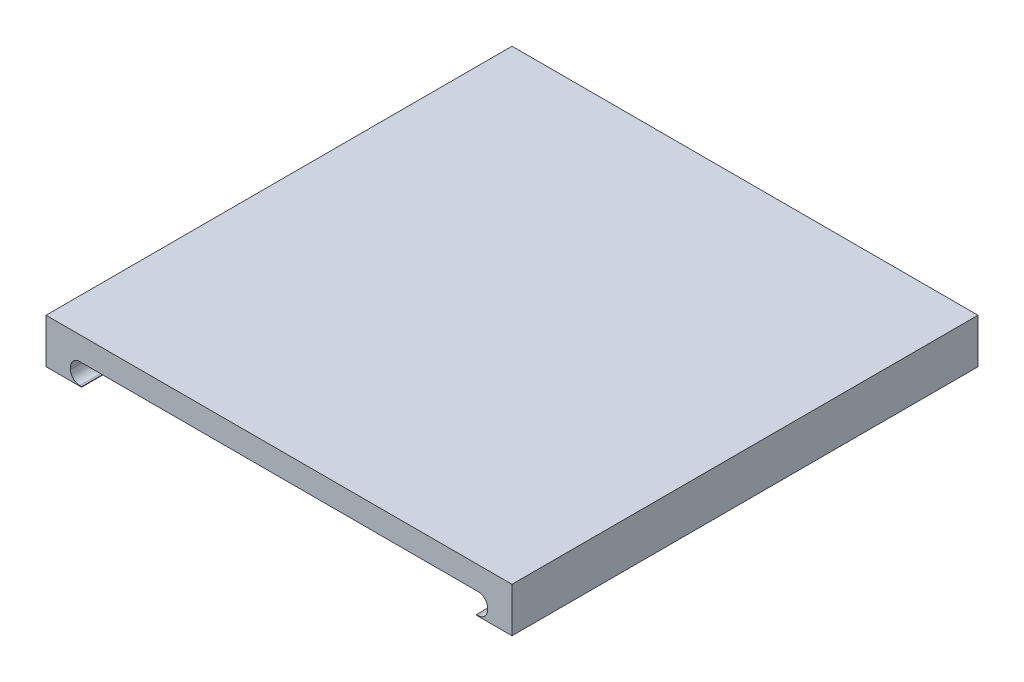
SolidWorks part; units mm, degrees
ref_plane "Front Plane" through (0, 0, 0) normal (0, 0, 1) x (1, 0, 0)
ref_plane "Top Plane" through (0, 0, 0) normal (0, 1, 0) x (1, 0, 0)
ref_plane "Right Plane" through (0, 0, 0) normal (1, 0, 0) x (0, 0, -1)
sketch "Sketch2" plane through (0, 0, 0) normal (0, 1, 0) x (1, 0, 0)
  line L7 (-25, -25) -> (25, -25)
  line L8 (-25, -25) -> (-25, 25)
  line L9 (-25, 25) -> (25, 25)
  line L10 (25, -25) -> (25, 25)
  line L11 (-25, -25) -> (25, 25) construction
  line L12 (-25, 25) -> (25, -25) construction
  point P0 (0, 0)
extrude "Boss-Extrude1" add sketch "Sketch2" along normal blind 5
sketch "Sketch4" plane through (0, 0, -25) normal (0, 0, -1) x (-1, 0, 0)
  line L2 (0, 0) -> (0, 5) construction
  line L3 (-25, 5) -> (25, 5) construction
sketch "Sketch6" plane through (0, 0, -25) normal (0, 0, -1) x (-1, 0, 0)
  line L0 (0, 0) -> (0, 1.25) construction
  line L13 (-25, 0) -> (25, 0) construction
  line L14 (-21.1824, 2.5) -> (21.1824, 2.5)
  line L15 (-21.1824, 2.5) -> (-21.1824, 0)
  line L16 (-21.1824, 0) -> (21.1824, 0)
  line L17 (21.1824, 2.5) -> (21.1824, 0)
  line L18 (-21.1824, 2.5) -> (21.1824, 0) construction
  line L19 (-21.1824, 0) -> (21.1824, 2.5) construction
extrude "Cut-Extrude1" cut sketch "Sketch6" against normal blind 50
sketch "Sketch9" plane through (0, 0, -25) normal (0, 0, -1) x (-1, 0, 0)
  line L1 (-21.1824, 2.5) -> (-22.371, 2.5)
  line L2 (-21.1824, 2.5) -> (-21.1824, 0.2785)
  line L3 (-21.1824, 0.2785) -> (-22.371, 0.2785)
  line L4 (-22.371, 2.5) -> (-22.371, 0.2785)
extrude "Cut-Extrude3" cut sketch "Sketch9" against normal blind 50
fillet "Fillet2" radius 1 1 edges at (22.371, 2.5, 0)
fillet "Fillet3" radius 1 1 edges at (22.371, 0.2785, 0)
sketch "Sketch11" plane through (0, 0, 25) normal (0, 0, 1) x (1, 0, 0)
  line L1 (-21.1824, 2.5) -> (-22.371, 2.5)
  line L2 (-21.1824, 2.5) -> (-21.1824, 0.2785)
  line L3 (-21.1824, 0.2785) -> (-22.371, 0.2785)
  line L4 (-22.371, 2.5) -> (-22.371, 0.2785)
extrude "Cut-Extrude4" cut sketch "Sketch11" against normal blind 50
fillet "Fillet5" radius 1 1 edges at (-22.371, 2.5, 0)
fillet "Fillet6" radius 1 1 edges at (-22.371, 0.2785, 0)
sketch "Sketch13" plane through (0, 0, 25) normal (0, 0, 1) x (1, 0, 0)
  line L0 (-21.1824, 0) -> (-21.1824, 0.2785) construction
  line L1 (-21.1824, 0.2182) -> (-25, 0.2182)
  line L2 (-21.1824, 0.2182) -> (-21.1824, 0)
  line L3 (-21.1824, 0) -> (-25, 0)
  line L4 (-25, 0.2182) -> (-25, 0)
sketch "Sketch14" plane through (0, 0, 25) normal (0, 0, 1) x (1, 0, 0)
  line L0 (-21.1824, 0.2182) -> (-25, 0.2182)
  line L1 (-21.1824, 0.2182) -> (-21.1824, 0)
  line L2 (-21.1824, 0) -> (-25, 0)
  line L3 (-25, 0.2182) -> (-25, 0)
extrude "Cut-Extrude5" cut sketch "Sketch14" against normal blind 50
sketch "Sketch15" plane through (0, 0, 25) normal (0, 0, 1) x (1, 0, 0)
  line L0 (25, 5) -> (25, 0) construction
  line L1 (21.1824, 0) -> (25, 0)
  line L2 (21.1824, 0) -> (21.1824, 0.2118)
  line L3 (21.1824, 0.2118) -> (25, 0.2118)
  line L4 (25, 0) -> (25, 0.2118)
sketch "Sketch16" plane through (0, 0, 25) normal (0, 0, 1) x (1, 0, 0)
  line L0 (21.1824, 0) -> (25, 0)
  line L1 (21.1824, 0) -> (21.1824, 0.2118)
  line L2 (21.1824, 0.2118) -> (25, 0.2118)
  line L3 (25, 0) -> (25, 0.2118)
extrude "Cut-Extrude6" cut sketch "Sketch16" against normal blind 50
